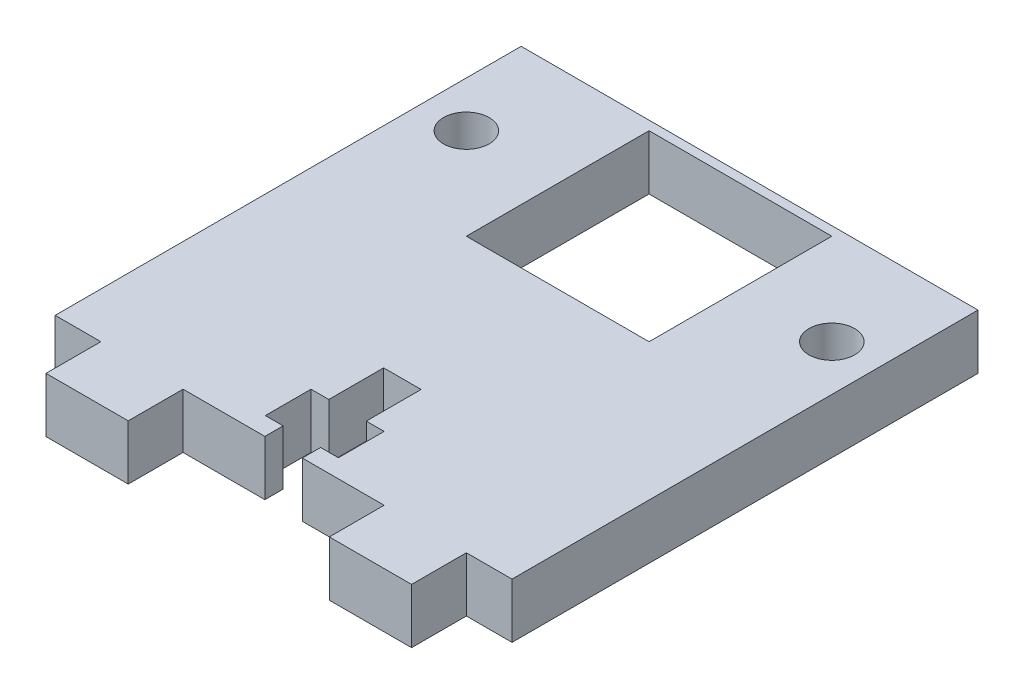
SolidWorks part; units mm, degrees
ref_plane "Front Plane" through (0, 0, 0) normal (0, 0, 1) x (1, 0, 0)
ref_plane "Top Plane" through (0, 0, 0) normal (0, 1, 0) x (1, 0, 0)
ref_plane "Right Plane" through (0, 0, 0) normal (1, 0, 0) x (0, 0, -1)
sketch "Sketch1" plane through (0, 0, 0) normal (0, 1, 0) x (1, 0, 0)
  line L0 (-25, 11) -> (25, 11)
  line L1 (25, 11) -> (25, -11)
  line L2 (-4, -33) -> (-2.05, -33)
  line L3 (25, -40) -> (25, -11)
  line L4 (25, -40) -> (20.0041, -40)
  line L5 (20.0041, -40) -> (20.0041, -46)
  line L6 (20.0041, -46) -> (11.0041, -46)
  line L7 (11.0041, -46) -> (11.0041, -40)
  line L8 (-11.0041, -40) -> (-2.05, -40)
  line L9 (-11.0041, -40) -> (-11.0041, -46)
  line L10 (-11.0041, -46) -> (-20.0041, -46)
  line L11 (-20.0041, -46) -> (-20.0041, -40)
  line L12 (-20.0041, -40) -> (-25, -40)
  line L13 (-25, 11) -> (-25, -11)
  line L14 (-25, -11) -> (-25, -40)
  line L16 (-25, 11) -> (25, -11) construction
  line L17 (-25, -11) -> (25, 11) construction
  line L18 (-2.05, -40) -> (-2.05, -38)
  line L19 (-2.05, -38) -> (-4, -38)
  line L20 (-4, -38) -> (-4, -33)
  line L22 (-2.05, -33) -> (-2.05, -27)
  line L23 (-2.05, -27) -> (2.05, -27)
  line L24 (2.05, -27) -> (2.05, -33)
  line L25 (2.05, -33) -> (4, -33)
  line L26 (4, -33) -> (4, -38)
  line L27 (4, -38) -> (2.05, -38)
  line L28 (2.05, -38) -> (2.05, -40)
  line L29 (2.05, -40) -> (11.0041, -40)
  dimension "D1" = 50
  dimension "D2" = 4.9959
  dimension "D3" = 9
  dimension "D4" = 29
  dimension "D5" = 22
  dimension "D6" = 6
  dimension "D7" = 8
  dimension "D8" = 5
  dimension "D9" = 13
  dimension "D10" = 2
  dimension "D11" = 4.1
sketch "Sketch2" plane through (0, 0, 0) normal (0, 1, 0) x (1, 0, 0)
  line L1 (-10, -10) -> (10, -10)
  line L2 (-10, -10) -> (-10, 10)
  line L3 (-10, 10) -> (10, 10)
  line L4 (10, -10) -> (10, 10)
  line L5 (-10, -10) -> (10, 10) construction
  line L6 (-10, 10) -> (10, -10) construction
  line L7 (0, 0) -> (-20, 0) construction
  line L8 (0, 0) -> (20, 0) construction
  circle A0 centre (-20, 0) radius 2.5
  circle A1 centre (20, 0) radius 2.5
  point P0 (0, 0)
  dimension "D3" = 5
  dimension "D1" = 20
  dimension "D2" = 20
extrude "Boss-Extrude1" add sketch "Sketch1" along normal blind 6 contours L0 L1 L3 L4 L5 L6 L7 L29 L28 L27 L26 L25 L24 L23 L22 L2 L20 L19 L18 L8 L9 L10 L11 L12 L14 L13
extrude "Cut-Extrude3" cut sketch "Sketch2" along normal blind 6
